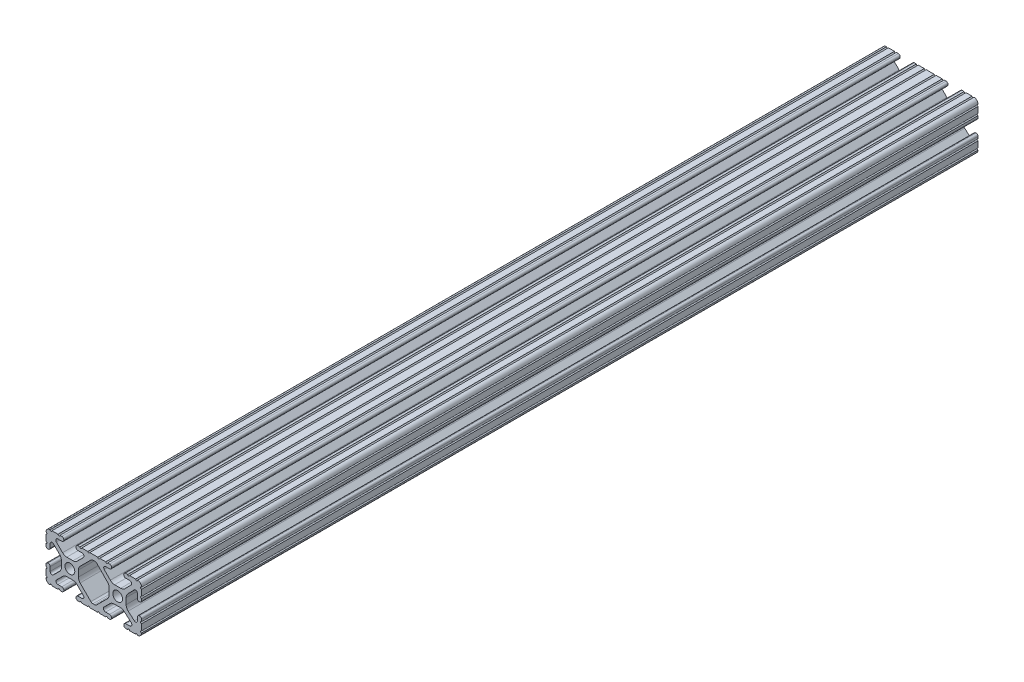
SolidWorks part; units mm, degrees
material "6061 Alloy"
ref_plane "Front Plane" through (0, 0, 0) normal (0, 0, 1) x (1, 0, 0)
ref_plane "Top Plane" through (0, 0, 0) normal (0, 1, 0) x (1, 0, 0)
ref_plane "Right Plane" through (0, 0, 0) normal (1, 0, 0) x (0, 0, -1)
sketch "Sketch1" plane through (0, 0, 0) normal (0, 0, 1) x (1, 0, 0)
  line L0 (-32.9707, 0) -> (32.2708, 0) construction
  line L1 (0, 12.7) -> (0, 0) construction
  line L2 (-12.7, 14.992) -> (-12.7, -12.6999) construction
  line L3 (12.7, 13.9801) -> (12.7, -13.3809) construction
  line L4 (-7.2595, -3.8694) -> (-1.5457, -9.5728)
  line L5 (1.5457, -9.5728) -> (7.2595, -3.8694)
  line L7 (-0.3952, 10.033) -> (0.5515, 10.033)
  line L9 (0.4332, -10.033) -> (-0.4332, -10.033)
  line L12 (8.1915, -1.6223) -> (8.1915, 1.6223)
  line L13 (7.2829, 3.8459) -> (1.6756, 9.5611)
  line L14 (-1.504, 9.5765) -> (-7.252, 3.8768)
  line L15 (-8.1915, 1.6223) -> (-8.1915, -1.6223)
  line L16 (22.2504, 12.7) -> (19.0331, 12.7)
  line L17 (18.0171, 12.7) -> (16.9875, 12.7)
  line L18 (15.9385, 11.651) -> (15.9385, 11.5392)
  line L19 (16.9875, 10.4902) -> (19.1164, 10.4902)
  line L20 (19.8441, 8.7652) -> (16.619, 5.4551)
  line L21 (14.3449, 4.4958) -> (11.0833, 4.4958)
  line L22 (8.817, 5.4472) -> (5.5642, 8.7627)
  line L23 (6.2894, 10.4902) -> (8.4125, 10.4902)
  line L24 (9.4615, 11.5392) -> (9.4615, 11.651)
  line L25 (8.4125, 12.7) -> (7.3829, 12.7)
  line L26 (6.3669, 12.7) -> (3.1496, 12.7)
  line L27 (2.1336, 12.7) -> (-2.1336, 12.7)
  line L28 (-3.1496, 12.7) -> (-6.3669, 12.7)
  line L29 (-7.3829, 12.7) -> (-8.4125, 12.7)
  line L30 (-9.4615, 11.651) -> (-9.4615, 11.5392)
  line L31 (-8.4125, 10.4902) -> (-6.2836, 10.4902)
  line L32 (-5.5326, 8.6661) -> (-8.81, 5.4163)
  line L33 (-11.0455, 4.4958) -> (-14.3545, 4.4958)
  line L34 (-16.59, 5.4163) -> (-19.8674, 8.6661)
  line L35 (-19.1164, 10.4902) -> (-16.9875, 10.4902)
  line L36 (-15.9385, 11.5392) -> (-15.9385, 11.651)
  line L37 (-16.9875, 12.7) -> (-18.0171, 12.7)
  line L38 (-19.0331, 12.7) -> (-22.2504, 12.7)
  line L39 (-25.4, 9.5504) -> (-25.4, 6.3331)
  line L40 (-25.4, 5.3171) -> (-25.4, 4.2375)
  line L41 (-24.401, 3.2385) -> (-24.2392, 3.2385)
  line L42 (-23.1902, 4.2875) -> (-23.1902, 6.3347)
  line L43 (-21.434, 7.0665) -> (-18.148, 3.8082)
  line L44 (-17.2085, 1.5536) -> (-17.2085, -1.6952)
  line L45 (-18.1405, -3.9423) -> (-21.4316, -7.2274)
  line L46 (-23.1902, -6.498) -> (-23.1902, -4.2875)
  line L47 (-24.2392, -3.2385) -> (-24.351, -3.2385)
  line L48 (-25.4, -4.2875) -> (-25.4, -5.3171)
  line L49 (-25.4, -6.3331) -> (-25.4, -9.5504)
  line L50 (-22.2504, -12.7) -> (-19.0331, -12.7)
  line L51 (-18.0171, -12.7) -> (-16.9875, -12.7)
  line L52 (-15.9384, -11.651) -> (-15.9384, -11.5392)
  line L53 (-16.9875, -10.4902) -> (-19.1164, -10.4902)
  line L54 (-19.8341, -8.7551) -> (-16.4966, -5.4237)
  line L55 (-14.2536, -4.4958) -> (-11.1464, -4.4958)
  line L56 (-8.9034, -5.4237) -> (-5.5659, -8.7551)
  line L57 (-6.2836, -10.4902) -> (-8.4125, -10.4902)
  line L58 (-9.4616, -11.5392) -> (-9.4616, -11.651)
  line L59 (-8.4125, -12.7) -> (-7.3829, -12.7)
  line L60 (-6.3669, -12.7) -> (-3.1496, -12.7)
  line L61 (-2.1336, -12.7) -> (2.1336, -12.7)
  line L62 (3.1496, -12.7) -> (6.3669, -12.7)
  line L63 (7.3829, -12.7) -> (8.4125, -12.7)
  line L64 (9.4616, -11.651) -> (9.4616, -11.5392)
  line L65 (8.4125, -10.4902) -> (6.2894, -10.4902)
  line L66 (5.4807, -8.5353) -> (8.5979, -5.4237)
  line L67 (10.8409, -4.4958) -> (14.1026, -4.4958)
  line L68 (16.1879, -5.2766) -> (19.8682, -8.4822)
  line L69 (19.1164, -10.4902) -> (16.9875, -10.4902)
  line L70 (15.9384, -11.5392) -> (15.9384, -11.651)
  line L71 (16.9875, -12.7) -> (18.0171, -12.7)
  line L72 (19.0331, -12.7) -> (22.2504, -12.7)
  line L73 (25.4, -9.5504) -> (25.4, -6.3331)
  line L74 (25.4, -5.3171) -> (25.4, -4.2375)
  line L75 (24.401, -3.2385) -> (24.1892, -3.2385)
  line L76 (23.1902, -4.2375) -> (23.1902, -6.1559)
  line L77 (21.584, -6.8869) -> (18.2982, -4.025)
  line L78 (17.2085, -1.6308) -> (17.2085, 1.6308)
  line L79 (18.1094, 3.8465) -> (21.5263, 7.3534)
  line L80 (23.1902, 6.6769) -> (23.1902, 4.2375)
  line L81 (24.1892, 3.2385) -> (24.401, 3.2385)
  line L82 (25.4, 4.2375) -> (25.4, 5.3171)
  line L83 (25.4, 6.3332) -> (25.4, 9.5504)
  circle A0 centre (-12.7, 0) radius 2.6035
  circle A1 centre (12.7, 0) radius 2.6035
  arc A2 (-0.3952, 10.033) -> (-1.504, 9.5765) centre (-0.3952, 8.4582) ccw
  arc A3 (0.5515, 10.033) -> (1.6756, 9.5611) centre (0.5515, 8.4582) cw
  arc A4 (-8.1915, -1.6223) -> (-7.2595, -3.8694) centre (-5.0165, -1.6223) ccw
  arc A5 (-0.4332, -10.033) -> (-1.5457, -9.5728) centre (-0.4332, -8.4582) cw
  arc A6 (7.2595, -3.8694) -> (8.1915, -1.6223) centre (5.0165, -1.6223) ccw
  arc A7 (8.1915, 1.6223) -> (7.2829, 3.8459) centre (5.0165, 1.6223) ccw
  arc A8 (0.4332, -10.033) -> (1.5457, -9.5728) centre (0.4332, -8.4582) ccw
  arc A9 (-7.252, 3.8768) -> (-8.1915, 1.6223) centre (-5.0165, 1.6223) ccw
  arc A16 (25.3998, 10.5664) -> (23.2664, 12.6998) centre (23.2918, 10.5918) ccw
  arc A17 (22.2504, 12.7) -> (23.2664, 12.6998) centre (22.7584, 12.7) ccw
  arc A18 (18.0171, 12.7) -> (19.0331, 12.7) centre (18.5251, 12.7) ccw
  arc A19 (16.9875, 12.7) -> (15.9385, 11.651) centre (16.9875, 11.651) ccw
  arc A20 (15.9385, 11.5392) -> (16.9875, 10.4902) centre (16.9875, 11.5392) ccw
  arc A21 (19.8441, 8.7652) -> (19.1164, 10.4902) centre (19.1164, 9.4742) ccw
  arc A22 (14.3449, 4.4958) -> (16.619, 5.4551) centre (14.3449, 7.6708) ccw
  arc A23 (8.817, 5.4472) -> (11.0833, 4.4958) centre (11.0833, 7.6708) ccw
  arc A24 (6.2894, 10.4902) -> (5.5642, 8.7627) centre (6.2894, 9.4742) ccw
  arc A25 (8.4125, 10.4902) -> (9.4615, 11.5392) centre (8.4125, 11.5392) ccw
  arc A26 (9.4615, 11.651) -> (8.4125, 12.7) centre (8.4125, 11.651) ccw
  arc A27 (6.3669, 12.7) -> (7.3829, 12.7) centre (6.8749, 12.7) ccw
  arc A28 (2.1336, 12.7) -> (3.1496, 12.7) centre (2.6416, 12.7) ccw
  arc A29 (-3.1496, 12.7) -> (-2.1336, 12.7) centre (-2.6416, 12.7) ccw
  arc A30 (-7.3829, 12.7) -> (-6.3669, 12.7) centre (-6.8749, 12.7) ccw
  arc A31 (-8.4125, 12.7) -> (-9.4615, 11.651) centre (-8.4125, 11.651) ccw
  arc A32 (-9.4615, 11.5392) -> (-8.4125, 10.4902) centre (-8.4125, 11.5392) ccw
  arc A33 (-5.5326, 8.6661) -> (-6.2836, 10.4902) centre (-6.2836, 9.4235) ccw
  arc A34 (-11.0455, 4.4958) -> (-8.81, 5.4163) centre (-11.0455, 7.6708) ccw
  arc A35 (-16.59, 5.4163) -> (-14.3545, 4.4958) centre (-14.3545, 7.6708) ccw
  arc A36 (-19.1164, 10.4902) -> (-19.8674, 8.6661) centre (-19.1164, 9.4235) ccw
  arc A37 (-16.9875, 10.4902) -> (-15.9385, 11.5392) centre (-16.9875, 11.5392) ccw
  arc A38 (-15.9385, 11.651) -> (-16.9875, 12.7) centre (-16.9875, 11.651) ccw
  arc A39 (-19.0331, 12.7) -> (-18.0171, 12.7) centre (-18.5251, 12.7) ccw
  arc A40 (-23.2664, 12.6998) -> (-22.2504, 12.7) centre (-22.7584, 12.7) ccw
  arc A41 (-23.2664, 12.6998) -> (-25.3998, 10.5664) centre (-23.2918, 10.5918) ccw
  arc A42 (-25.4, 9.5504) -> (-25.3998, 10.5664) centre (-25.4, 10.0584) ccw
  arc A43 (-25.4, 5.3171) -> (-25.4, 6.3331) centre (-25.4, 5.8251) ccw
  arc A44 (-25.4, 4.2375) -> (-24.401, 3.2385) centre (-24.401, 4.2375) ccw
  arc A45 (-24.2392, 3.2385) -> (-23.1902, 4.2875) centre (-24.2392, 4.2875) ccw
  arc A46 (-21.434, 7.0665) -> (-23.1902, 6.3347) centre (-22.1596, 6.3347) ccw
  arc A47 (-17.2085, 1.5536) -> (-18.148, 3.8082) centre (-20.3835, 1.5536) ccw
  arc A48 (-18.1405, -3.9423) -> (-17.2085, -1.6952) centre (-20.3835, -1.6952) ccw
  arc A49 (-23.1902, -6.498) -> (-21.4316, -7.2274) centre (-22.1596, -6.498) ccw
  arc A50 (-23.1902, -4.2875) -> (-24.2392, -3.2385) centre (-24.2392, -4.2875) ccw
  arc A51 (-24.351, -3.2385) -> (-25.4, -4.2875) centre (-24.351, -4.2875) ccw
  arc A52 (-25.4, -6.3331) -> (-25.4, -5.3171) centre (-25.4, -5.8251) ccw
  arc A53 (-25.3998, -10.5664) -> (-25.4, -9.5504) centre (-25.4, -10.0584) ccw
  arc A54 (-25.3998, -10.5664) -> (-23.2664, -12.6998) centre (-23.2918, -10.5918) ccw
  arc A55 (-22.2504, -12.7) -> (-23.2664, -12.6998) centre (-22.7584, -12.7) ccw
  arc A56 (-18.0171, -12.7) -> (-19.0331, -12.7) centre (-18.5251, -12.7) ccw
  arc A57 (-16.9875, -12.7) -> (-15.9384, -11.651) centre (-16.9875, -11.651) ccw
  arc A58 (-15.9384, -11.5392) -> (-16.9875, -10.4902) centre (-16.9875, -11.5392) ccw
  arc A59 (-19.8341, -8.7551) -> (-19.1164, -10.4902) centre (-19.1164, -9.4742) ccw
  arc A60 (-14.2536, -4.4958) -> (-16.4966, -5.4237) centre (-14.2536, -7.6708) ccw
  arc A61 (-8.9034, -5.4237) -> (-11.1464, -4.4958) centre (-11.1464, -7.6708) ccw
  arc A62 (-6.2836, -10.4902) -> (-5.5659, -8.7551) centre (-6.2836, -9.4742) ccw
  arc A63 (-8.4125, -10.4902) -> (-9.4616, -11.5392) centre (-8.4125, -11.5392) ccw
  arc A64 (-9.4616, -11.651) -> (-8.4125, -12.7) centre (-8.4125, -11.651) ccw
  arc A65 (-6.3669, -12.7) -> (-7.3829, -12.7) centre (-6.8749, -12.7) ccw
  arc A66 (-2.1336, -12.7) -> (-3.1496, -12.7) centre (-2.6416, -12.7) ccw
  arc A67 (3.1496, -12.7) -> (2.1336, -12.7) centre (2.6416, -12.7) ccw
  arc A68 (7.3829, -12.7) -> (6.3669, -12.7) centre (6.8749, -12.7) ccw
  arc A69 (8.4125, -12.7) -> (9.4616, -11.651) centre (8.4125, -11.651) ccw
  arc A70 (9.4616, -11.5392) -> (8.4125, -10.4902) centre (8.4125, -11.5392) ccw
  arc A71 (5.4807, -8.5353) -> (6.2894, -10.4902) centre (6.2894, -9.3455) ccw
  arc A72 (10.8409, -4.4958) -> (8.5979, -5.4237) centre (10.8409, -7.6708) ccw
  arc A73 (16.1879, -5.2766) -> (14.1026, -4.4958) centre (14.1026, -7.6708) ccw
  arc A74 (19.1164, -10.4902) -> (19.8682, -8.4822) centre (19.1164, -9.3455) ccw
  arc A75 (16.9875, -10.4902) -> (15.9384, -11.5392) centre (16.9875, -11.5392) ccw
  arc A76 (15.9384, -11.651) -> (16.9875, -12.7) centre (16.9875, -11.651) ccw
  arc A77 (19.0331, -12.7) -> (18.0171, -12.7) centre (18.5251, -12.7) ccw
  arc A78 (23.2664, -12.6998) -> (22.2504, -12.7) centre (22.7584, -12.7) ccw
  arc A79 (23.2664, -12.6998) -> (25.3998, -10.5664) centre (23.2918, -10.5918) ccw
  arc A80 (25.4, -9.5504) -> (25.3998, -10.5664) centre (25.4, -10.0584) ccw
  arc A81 (25.4, -5.3171) -> (25.4, -6.3331) centre (25.4, -5.8251) ccw
  arc A82 (25.4, -4.2375) -> (24.401, -3.2385) centre (24.401, -4.2375) ccw
  arc A83 (24.1892, -3.2385) -> (23.1902, -4.2375) centre (24.1892, -4.2375) ccw
  arc A84 (21.584, -6.8869) -> (23.1902, -6.1559) centre (22.2207, -6.1559) ccw
  arc A85 (17.2085, -1.6308) -> (18.2982, -4.025) centre (20.3835, -1.6308) ccw
  arc A86 (18.1094, 3.8465) -> (17.2085, 1.6308) centre (20.3835, 1.6308) ccw
  arc A87 (23.1902, 6.6769) -> (21.5263, 7.3534) centre (22.2207, 6.6769) ccw
  arc A88 (23.1902, 4.2375) -> (24.1892, 3.2385) centre (24.1892, 4.2375) ccw
  arc A89 (24.401, 3.2385) -> (25.4, 4.2375) centre (24.401, 4.2375) ccw
  arc A90 (25.4, 6.3332) -> (25.4, 5.3171) centre (25.4, 5.8251) ccw
  arc A91 (25.3998, 10.5664) -> (25.4, 9.5504) centre (25.4, 10.0584) ccw
  dimension "D1" = 5.207
  dimension "D6" = 6.477
  dimension "D7" = 14.859
  dimension "D14" = 1.5748
  dimension "D16" = 1.5748
  dimension "D15" = 3.175
  dimension "D2" = 25.4
  dimension "D3" = 50.8
  dimension "D4" = 25.4
  dimension "D5" = 8.2042
  dimension "D8" = 2.2098
  dimension "D9" = 2.2098
  dimension "D10" = 2.2098
  dimension "D11" = 2.2098
  dimension "D12" = 2.2098
  dimension "D13" = 6.477
extrude "Extrude1" add sketch "Sketch1" against normal blind 444.754
